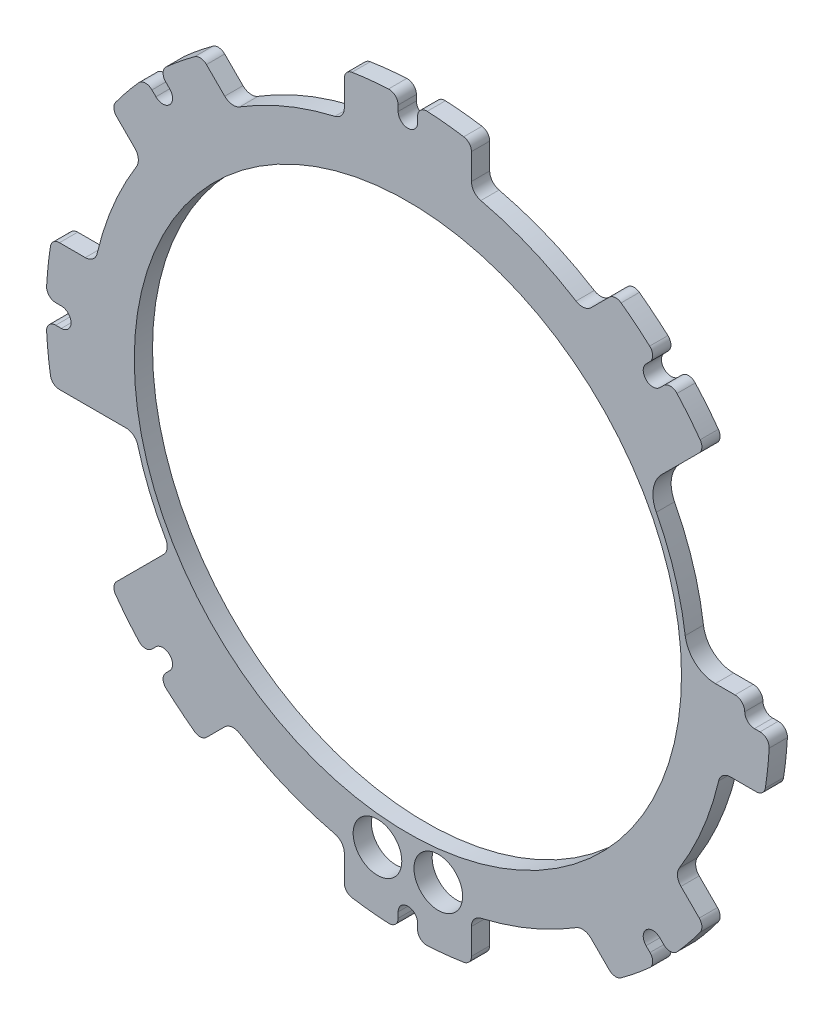
SolidWorks part; units mm, degrees
material "A-Glasfaser"
ref_plane "Ebene vorne" through (0, 0, 0) normal (0, 0, 1) x (1, 0, 0)
ref_plane "Ebene oben" through (0, 0, 0) normal (0, 1, 0) x (1, 0, 0)
ref_plane "Ebene rechts" through (0, 0, 0) normal (1, 0, 0) x (0, 0, -1)
sketch "Skizze1" plane through (0, 0, 0) normal (0, 0, 1) x (1, 0, 0)
  line L0 (10.4571, 53.0572) -> (10.4571, 57.3042)
  line L1 (1.6, 57.9171) -> (1.6, 57)
  line L2 (-10.4571, 57.3042) -> (-10.4571, 53.0572)
  line L3 (0, 0) -> (20.0909, 48.5037) construction
  line L4 (0, 0) -> (-20.0909, 48.5037) construction
  line L5 (-1.6, 57) -> (-1.6, 57.9171)
  line L6 (0, 57) -> (0, 0) construction
  line L7 (44.9114, 30.1228) -> (47.9145, 33.1259)
  line L8 (42.0849, 39.8222) -> (41.4365, 39.1737)
  line L9 (33.1259, 47.9145) -> (30.1228, 44.9114)
  line L10 (39.1737, 41.4365) -> (39.8222, 42.0849)
  line L11 (0, 0) -> (48.5037, 20.0909) construction
  line L12 (0, 0) -> (20.0909, 48.5037) construction
  line L13 (40.3051, 40.3051) -> (0, 0) construction
  line L14 (53.0572, -10.4571) -> (57.3042, -10.4571)
  line L15 (57.9171, -1.6) -> (57, -1.6)
  line L16 (57.3042, 10.4571) -> (53.0572, 10.4571)
  line L17 (57, 1.6) -> (57.9171, 1.6)
  line L18 (0, 0) -> (48.5037, -20.0909) construction
  line L19 (0, 0) -> (48.5037, 20.0909) construction
  line L20 (57, 0) -> (0, 0) construction
  line L21 (30.1228, -44.9114) -> (33.1259, -47.9145)
  line L22 (39.8222, -42.0849) -> (39.1737, -41.4365)
  line L23 (47.9145, -33.1259) -> (44.9114, -30.1228)
  line L24 (41.4365, -39.1737) -> (42.0849, -39.8222)
  line L25 (0, 0) -> (20.0909, -48.5037) construction
  line L26 (0, 0) -> (48.5037, -20.0909) construction
  line L27 (40.3051, -40.3051) -> (0, 0) construction
  line L28 (-10.4571, -53.0572) -> (-10.4571, -57.3042)
  line L29 (-1.6, -57.9171) -> (-1.6, -57)
  line L30 (10.4571, -57.3042) -> (10.4571, -53.0572)
  line L31 (1.6, -57) -> (1.6, -57.9171)
  line L32 (0, 0) -> (-20.0909, -48.5037) construction
  line L33 (0, 0) -> (20.0909, -48.5037) construction
  line L34 (0, -57) -> (0, 0) construction
  line L35 (-44.9114, -30.1228) -> (-47.9145, -33.1259)
  line L36 (-42.0849, -39.8222) -> (-41.4365, -39.1737)
  line L37 (-33.1259, -47.9145) -> (-30.1228, -44.9114)
  line L38 (-39.1737, -41.4365) -> (-39.8222, -42.0849)
  line L39 (0, 0) -> (-48.5037, -20.0909) construction
  line L40 (0, 0) -> (-20.0909, -48.5037) construction
  line L42 (-53.0572, 10.4571) -> (-57.3042, 10.4571)
  line L43 (-57.9171, 1.6) -> (-57, 1.6)
  line L44 (-57.3042, -10.4571) -> (-53.0572, -10.4571)
  line L45 (-57, -1.6) -> (-57.9171, -1.6)
  line L46 (0, 0) -> (-48.5037, 20.0909) construction
  line L47 (0, 0) -> (-48.5037, -20.0909) construction
  line L48 (-57, 0) -> (0, 0) construction
  line L49 (-30.1228, 44.9114) -> (-33.1259, 47.9145)
  line L50 (-39.8222, 42.0849) -> (-39.1737, 41.4365)
  line L51 (-47.9145, 33.1259) -> (-44.9114, 30.1228)
  line L52 (-41.4365, 39.1737) -> (-42.0849, 39.8222)
  line L53 (0, 0) -> (-20.0909, 48.5037) construction
  line L54 (0, 0) -> (-48.5037, 20.0909) construction
  line L55 (-40.3051, 40.3051) -> (0, 0) construction
  line L61 (-40.3051, -40.3051) -> (0, 0) construction
  arc A0 (10.4571, 57.3042) -> (9.1888, 58.7862) centre (8.9571, 57.3042) ccw
  arc A1 (-9.1888, 58.7862) -> (-10.4571, 57.3042) centre (-8.9571, 57.3042) ccw
  arc A2 (-10.4571, 53.0572) -> (-12, 51.1102) centre (-12.4571, 53.0572) cw
  arc A3 (-12, 51.1102) -> (-20.0909, 48.5037) centre (0, 0) ccw
  arc A4 (10.4571, 53.0572) -> (12, 51.1102) centre (12.4571, 53.0572) ccw
  arc A5 (12, 51.1102) -> (20.0909, 48.5037) centre (0, 0) cw
  arc A6 (-9.1888, 58.7862) -> (-3.1802, 59.415) centre (0, 0) cw
  arc A7 (-1.6, 57) -> (1.6, 57) centre (0, 57) ccw
  arc A8 (1.6, 57.9171) -> (3.1802, 59.415) centre (3.1, 57.9171) cw
  arc A9 (-1.6, 57.9171) -> (-3.1802, 59.415) centre (-3.1, 57.9171) ccw
  arc A10 (3.1802, 59.415) -> (9.1888, 58.7862) centre (0, 0) cw
  arc A11 (47.9145, 33.1259) -> (48.0656, 35.0707) centre (46.8538, 34.1865) ccw
  arc A12 (35.0707, 48.0656) -> (33.1259, 47.9145) centre (34.1865, 46.8538) ccw
  arc A13 (30.1228, 44.9114) -> (27.6551, 44.6256) centre (28.7086, 46.3257) cw
  arc A14 (27.6551, 44.6256) -> (20.0909, 48.5037) centre (0, 0) ccw
  arc A15 (44.9114, 30.1228) -> (44.6256, 27.6551) centre (46.3257, 28.7086) ccw
  arc A16 (44.6256, 27.6551) -> (48.5037, 20.0909) centre (0, 0) cw
  arc A17 (35.0707, 48.0656) -> (39.764, 44.2614) centre (0, 0) cw
  arc A18 (39.1737, 41.4365) -> (41.4365, 39.1737) centre (40.3051, 40.3051) ccw
  arc A19 (42.0849, 39.8222) -> (44.2614, 39.764) centre (43.1456, 38.7615) cw
  arc A20 (39.8222, 42.0849) -> (39.764, 44.2614) centre (38.7615, 43.1456) ccw
  arc A21 (44.2614, 39.764) -> (48.0656, 35.0707) centre (0, 0) cw
  arc A22 (57.3042, -10.4571) -> (58.7862, -9.1888) centre (57.3042, -8.9571) ccw
  arc A23 (58.7862, 9.1888) -> (57.3042, 10.4571) centre (57.3042, 8.9571) ccw
  arc A24 (53.0572, 10.4571) -> (51.1102, 12) centre (53.0572, 12.4571) cw
  arc A25 (51.1102, 12) -> (48.5037, 20.0909) centre (0, 0) ccw
  arc A26 (53.0572, -10.4571) -> (51.1102, -12) centre (53.0572, -12.4571) ccw
  arc A27 (51.1102, -12) -> (48.5037, -20.0909) centre (0, 0) cw
  arc A28 (58.7862, 9.1888) -> (59.415, 3.1802) centre (0, 0) cw
  arc A29 (57, 1.6) -> (57, -1.6) centre (57, 0) ccw
  arc A30 (57.9171, -1.6) -> (59.415, -3.1802) centre (57.9171, -3.1) cw
  arc A31 (57.9171, 1.6) -> (59.415, 3.1802) centre (57.9171, 3.1) ccw
  arc A32 (59.415, -3.1802) -> (58.7862, -9.1888) centre (0, 0) cw
  arc A33 (33.1259, -47.9145) -> (35.0707, -48.0656) centre (34.1865, -46.8538) ccw
  arc A34 (48.0656, -35.0707) -> (47.9145, -33.1259) centre (46.8538, -34.1865) ccw
  arc A35 (44.9114, -30.1228) -> (44.6256, -27.6551) centre (46.3257, -28.7086) cw
  arc A36 (44.6256, -27.6551) -> (48.5037, -20.0909) centre (0, 0) ccw
  arc A37 (30.1228, -44.9114) -> (27.6551, -44.6256) centre (28.7086, -46.3257) ccw
  arc A38 (27.6551, -44.6256) -> (20.0909, -48.5037) centre (0, 0) cw
  arc A39 (48.0656, -35.0707) -> (44.2614, -39.764) centre (0, 0) cw
  arc A40 (41.4365, -39.1737) -> (39.1737, -41.4365) centre (40.3051, -40.3051) ccw
  arc A41 (39.8222, -42.0849) -> (39.764, -44.2614) centre (38.7615, -43.1456) cw
  arc A42 (42.0849, -39.8222) -> (44.2614, -39.764) centre (43.1456, -38.7615) ccw
  arc A43 (39.764, -44.2614) -> (35.0707, -48.0656) centre (0, 0) cw
  arc A44 (-10.4571, -57.3042) -> (-9.1888, -58.7862) centre (-8.9571, -57.3042) ccw
  arc A45 (9.1888, -58.7862) -> (10.4571, -57.3042) centre (8.9571, -57.3042) ccw
  arc A46 (10.4571, -53.0572) -> (12, -51.1102) centre (12.4571, -53.0572) cw
  arc A47 (12, -51.1102) -> (20.0909, -48.5037) centre (0, 0) ccw
  arc A48 (-10.4571, -53.0572) -> (-12, -51.1102) centre (-12.4571, -53.0572) ccw
  arc A49 (-12, -51.1102) -> (-20.0909, -48.5037) centre (0, 0) cw
  arc A50 (9.1888, -58.7862) -> (3.1802, -59.415) centre (0, 0) cw
  arc A51 (1.6, -57) -> (-1.6, -57) centre (0, -57) ccw
  arc A52 (-1.6, -57.9171) -> (-3.1802, -59.415) centre (-3.1, -57.9171) cw
  arc A53 (1.6, -57.9171) -> (3.1802, -59.415) centre (3.1, -57.9171) ccw
  arc A54 (-3.1802, -59.415) -> (-9.1888, -58.7862) centre (0, 0) cw
  arc A55 (-47.9145, -33.1259) -> (-48.0656, -35.0707) centre (-46.8538, -34.1865) ccw
  arc A56 (-35.0707, -48.0656) -> (-33.1259, -47.9145) centre (-34.1865, -46.8538) ccw
  arc A57 (-30.1228, -44.9114) -> (-27.6551, -44.6256) centre (-28.7086, -46.3257) cw
  arc A58 (-27.6551, -44.6256) -> (-20.0909, -48.5037) centre (0, 0) ccw
  arc A59 (-44.9114, -30.1228) -> (-44.6256, -27.6551) centre (-46.3257, -28.7086) ccw
  arc A60 (-44.6256, -27.6551) -> (-48.5037, -20.0909) centre (0, 0) cw
  arc A61 (-35.0707, -48.0656) -> (-39.764, -44.2614) centre (0, 0) cw
  arc A62 (-39.1737, -41.4365) -> (-41.4365, -39.1737) centre (-40.3051, -40.3051) ccw
  arc A63 (-42.0849, -39.8222) -> (-44.2614, -39.764) centre (-43.1456, -38.7615) cw
  arc A64 (-39.8222, -42.0849) -> (-39.764, -44.2614) centre (-38.7615, -43.1456) ccw
  arc A65 (-44.2614, -39.764) -> (-48.0656, -35.0707) centre (0, 0) cw
  arc A66 (-57.3042, 10.4571) -> (-58.7862, 9.1888) centre (-57.3042, 8.9571) ccw
  arc A67 (-58.7862, -9.1888) -> (-57.3042, -10.4571) centre (-57.3042, -8.9571) ccw
  arc A68 (-53.0572, -10.4571) -> (-51.1102, -12) centre (-53.0572, -12.4571) cw
  arc A69 (-51.1102, -12) -> (-48.5037, -20.0909) centre (0, 0) ccw
  arc A70 (-53.0572, 10.4571) -> (-51.1102, 12) centre (-53.0572, 12.4571) ccw
  arc A71 (-51.1102, 12) -> (-48.5037, 20.0909) centre (0, 0) cw
  arc A72 (-58.7862, -9.1888) -> (-59.415, -3.1802) centre (0, 0) cw
  arc A73 (-57, -1.6) -> (-57, 1.6) centre (-57, 0) ccw
  arc A74 (-57.9171, 1.6) -> (-59.415, 3.1802) centre (-57.9171, 3.1) cw
  arc A75 (-57.9171, -1.6) -> (-59.415, -3.1802) centre (-57.9171, -3.1) ccw
  arc A76 (-59.415, 3.1802) -> (-58.7862, 9.1888) centre (0, 0) cw
  arc A77 (-33.1259, 47.9145) -> (-35.0707, 48.0656) centre (-34.1865, 46.8538) ccw
  arc A78 (-48.0656, 35.0707) -> (-47.9145, 33.1259) centre (-46.8538, 34.1865) ccw
  arc A79 (-44.9114, 30.1228) -> (-44.6256, 27.6551) centre (-46.3257, 28.7086) cw
  arc A80 (-44.6256, 27.6551) -> (-48.5037, 20.0909) centre (0, 0) ccw
  arc A81 (-30.1228, 44.9114) -> (-27.6551, 44.6256) centre (-28.7086, 46.3257) ccw
  arc A82 (-27.6551, 44.6256) -> (-20.0909, 48.5037) centre (0, 0) cw
  arc A83 (-48.0656, 35.0707) -> (-44.2614, 39.764) centre (0, 0) cw
  arc A84 (-41.4365, 39.1737) -> (-39.1737, 41.4365) centre (-40.3051, 40.3051) ccw
  arc A85 (-39.8222, 42.0849) -> (-39.764, 44.2614) centre (-38.7615, 43.1456) cw
  arc A86 (-42.0849, 39.8222) -> (-44.2614, 39.764) centre (-43.1456, 38.7615) ccw
  arc A87 (-39.764, 44.2614) -> (-35.0707, 48.0656) centre (0, 0) cw
  dimension "D2" = 1.5
  dimension "D4" = 52.5
  dimension "D3" = 59.5
  dimension "D6" = 3.2
  dimension "D7" = 2
  dimension "D1" = 24
  dimension "D5" = 45
  dimension "D8" = 57
  dimension "D9" = 8
extrude "Aufsatz-Linear austragen1" add sketch "Skizze1" along normal blind 3 contours A87 A85 L50 A84 L52 A86 A83 A78 L51 A79 A80 A71 A70 L42 A66 A76 A74 L43 A73 L45 A75 A72 A67 L44 A68 A69 A60 A59 L35 A55 A65 A63 L36 A62 L38 A64 A61 A56 L37 A57 A58 A49 A48 L28 A44 A54 A52 L29 A51 L31 A53
sketch "Skizze2" plane through (0, 0, 3) normal (0, 0, 1) x (1, 0, 0)
  circle A0 centre (0, 0) radius 45
  dimension "D1" = 90
extrude "Schnitt-Linear austragen1" cut sketch "Skizze2" against normal through all
sketch "Skizze4" plane through (0, 0, 3) normal (0, 0, 1) x (1, 0, 0)
  line L0 (0, 0) -> (0, -55.4) construction
  line L1 (-5, -49.5) -> (5, -49.5) construction
  circle A4 centre (-5, -49.5) radius 4
  circle A5 centre (5, -49.5) radius 4
  arc A6 (1.6, -57) -> (-1.6, -57) centre (0, -57) ccw construction
  point P9 (0, -49.5)
  dimension "D1" = 10
  dimension "D3" = 8
  dimension "D4" = 49.5
extrude "Schnitt-Linear austragen3" cut sketch "Skizze4" against normal through all
sketch "Skizze5" plane through (0, 0, 3) normal (0, 0, 1) x (1, 0, 0)
  line L0 (-53.0572, -10.4571) -> (-44.9114, -30.1228)
  line L1 (44.9114, 30.1228) -> (41.7606, 26.9719)
  line L3 (-44.9114, -30.1228) -> (-47.9145, -33.1259) construction
  line L5 (44.9114, 30.1228) -> (47.9145, 33.1259) construction
  line L6 (-44.9114, -30.1228) -> (-40.1725, -25.3839)
  line L7 (-46.3554, -10.4571) -> (-53.0572, -10.4571)
  line L8 (-57.3042, -10.4571) -> (-53.0572, -10.4571) construction
  line L9 (50.5711, 1.6) -> (53.8, 1.6)
  line L10 (57.3042, 10.4571) -> (53.0572, 10.4571) construction
  line L11 (59.415, 3.1802) -> (57.3093, 42.5206)
  line L12 (57.3093, 42.5206) -> (44.9114, 30.1228)
  line L14 (57, 1.6) -> (57.9171, 1.6) construction
  line L15 (57, 1.6) -> (57.9171, 1.6)
  arc A4 (41.7606, 26.9719) -> (40.8553, 21.1387) centre (45.2961, 23.4364) ccw
  arc A6 (40.8553, 21.1387) -> (45.6132, 5.9529) centre (0, 0) cw
  arc A8 (-40.1725, -25.3839) -> (-39.8539, -22.9709) centre (-41.5867, -23.9697) ccw
  circle A10 centre (0, 0) radius 45 construction
  arc A11 (-39.8539, -22.9709) -> (-44.4239, -11.9381) centre (0, 0) cw
  arc A12 (-44.4239, -11.9381) -> (-46.3554, -10.4571) centre (-46.3554, -12.4571) ccw
  arc A14 (57.9171, 1.6) -> (59.415, 3.1802) centre (57.9171, 3.1) ccw construction
  arc A15 (59.415, 3.1802) -> (58.7862, 9.1888) centre (0, 0) ccw construction
  arc A17 (50.5711, 1.6) -> (45.6132, 5.9529) centre (50.5711, 6.6) cw
  arc A18 (57, 1.6) -> (57, -1.6) centre (57, 0) ccw construction
  arc A19 (57, 1.6) -> (55.4, 0) centre (57, 0) ccw
  arc A20 (57.9171, 1.6) -> (59.415, 3.1802) centre (57.9171, 3.1) ccw
  arc A21 (53.8, 1.6) -> (55.4, 0) centre (53.8, 0) cw
  arc A22 (55.4, 0) -> (57, -1.6) centre (57, 0) ccw construction
  point P18 (53.8, 1.6)
  point P30 (0, 0)
  point P36 (53.8, 1.6)
  point P37 (55.4134, -0.2066)
  point P38 (55.4271, 0.2931)
  point P40 (55.4, 0)
  dimension "D1" = 5
  dimension "D2" = 46
  dimension "D3" = 1
  dimension "D4" = 2
extrude "Schnitt-Linear austragen4" cut sketch "Skizze5" against normal through all
